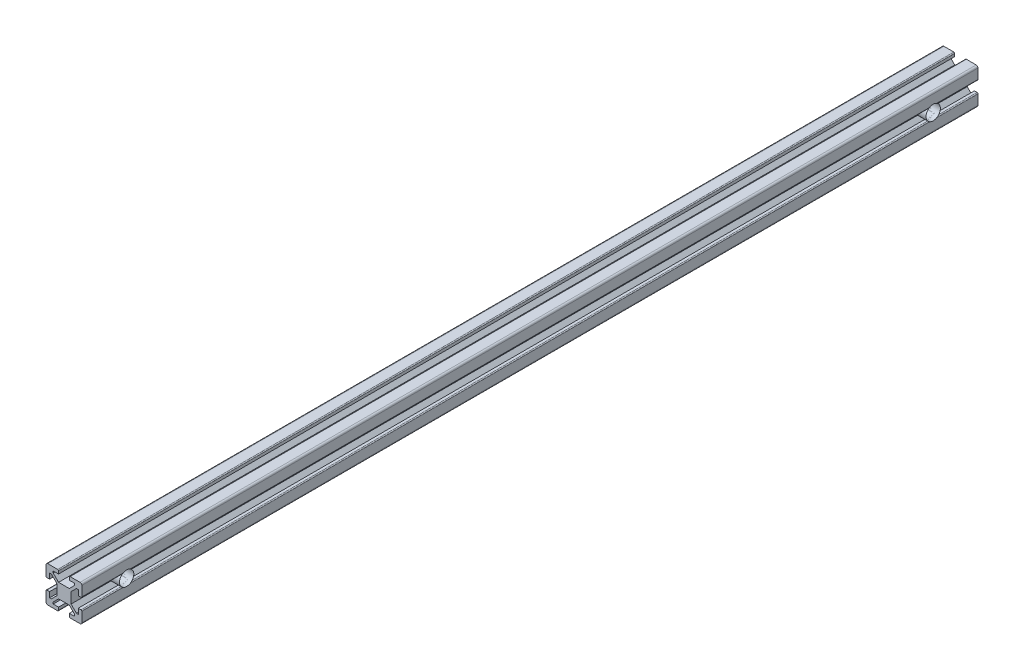
SolidWorks part; units mm, degrees
material "Lega 6061"
ref_plane "Piano frontale" through (0, 0, 0) normal (0, 0, 1) x (1, 0, 0)
ref_plane "Piano superiore" through (0, 0, 0) normal (0, 1, 0) x (1, 0, 0)
ref_plane "Piano destro" through (0, 0, 0) normal (1, 0, 0) x (0, 0, -1)
sketch "Schizzo1" plane through (0, 0, 0) normal (0, 0, 1) x (1, 0, 0)
  line L0 (0, 0) -> (-3.6, 0) construction
  line L1 (0, 0) -> (0, 3.6) construction
  line L3 (-4, -3) -> (-4, 3)
  line L4 (-4, 3) -> (-7, 6)
  line L5 (-7, 6) -> (-8, 6)
  line L6 (-8, 6) -> (-8, 3)
  line L7 (-8, 3) -> (-9.5, 3)
  line L8 (-10, 3.5) -> (-10, 9)
  line L9 (0, 0) -> (-10, 10) construction
  line L12 (-3, 4) -> (-6, 7)
  line L13 (-6, 7) -> (-6, 8)
  line L14 (-6, 8) -> (-3, 8)
  line L15 (-3, 8) -> (-3, 9.5)
  line L16 (-3.5, 10) -> (-9, 10)
  line L17 (0, 0) -> (-10, -10) construction
  line L18 (-3.5, -10) -> (-9, -10)
  line L19 (-3, -8) -> (-3, -9.5)
  line L20 (-6, -8) -> (-3, -8)
  line L21 (-6, -7) -> (-6, -8)
  line L22 (-3, -4) -> (-6, -7)
  line L25 (-10, -3.5) -> (-10, -9)
  line L26 (-8, -3) -> (-9.5, -3)
  line L27 (-8, -6) -> (-8, -3)
  line L28 (-7, -6) -> (-8, -6)
  line L29 (-4, -3) -> (-7, -6)
  line L32 (0, 0) -> (10, -10) construction
  line L33 (0, 0) -> (10, 10) construction
  line L36 (4, -3) -> (7, -6)
  line L37 (7, -6) -> (8, -6)
  line L38 (8, -6) -> (8, -3)
  line L39 (8, -3) -> (9.5, -3)
  line L40 (10, -3.5) -> (10, -9)
  line L43 (3, -4) -> (6, -7)
  line L44 (6, -7) -> (6, -8)
  line L45 (6, -8) -> (3, -8)
  line L46 (3, -8) -> (3, -9.5)
  line L47 (3.5, -10) -> (9, -10)
  line L48 (3.5, 10) -> (9, 10)
  line L49 (3, 8) -> (3, 9.5)
  line L50 (6, 8) -> (3, 8)
  line L51 (6, 7) -> (6, 8)
  line L52 (3, 4) -> (6, 7)
  line L55 (10, 3.5) -> (10, 9)
  line L56 (8, 3) -> (9.5, 3)
  line L57 (8, 6) -> (8, 3)
  line L58 (7, 6) -> (8, 6)
  line L59 (4, 3) -> (7, 6)
  line L60 (-3, 4) -> (3, 4)
  line L62 (-3, -4) -> (3, -4)
  line L63 (4, 3) -> (4, -3)
  arc A0 (-10, 9) -> (-9, 10) centre (-9, 9) cw
  arc A1 (-3, 9.5) -> (-3.5, 10) centre (-3.5, 9.5) ccw
  arc A2 (-9.5, 3) -> (-10, 3.5) centre (-9.5, 3.5) cw
  arc A3 (-9.5, -3) -> (-10, -3.5) centre (-9.5, -3.5) ccw
  arc A4 (-3, -9.5) -> (-3.5, -10) centre (-3.5, -9.5) cw
  arc A5 (-10, -9) -> (-9, -10) centre (-9, -9) ccw
  arc A6 (10, -9) -> (9, -10) centre (9, -9) cw
  arc A7 (3, -9.5) -> (3.5, -10) centre (3.5, -9.5) ccw
  arc A8 (9.5, -3) -> (10, -3.5) centre (9.5, -3.5) cw
  arc A9 (9.5, 3) -> (10, 3.5) centre (9.5, 3.5) ccw
  arc A10 (3, 9.5) -> (3.5, 10) centre (3.5, 9.5) cw
  arc A11 (10, 9) -> (9, 10) centre (9, 9) ccw
  point P24 (-3, 10)
  point P27 (-10, 3)
  point P49 (-10, -3)
  point P50 (-3, -10)
  point P92 (3, -10)
  point P93 (10, -3)
  point P94 (10, 3)
  point P95 (3, 10)
  dimension "D2" = 1
  dimension "D12" = 0.5
  dimension "D3" = 8
  dimension "D6" = 6
  dimension "D7" = 12
  dimension "D8" = 20
  dimension "D9" = 2
  dimension "D10" = 4
  dimension "D11" = 45
extrude "Estrusione-Estrusione1" add sketch "Schizzo1" along normal blind 500
sketch "Schizzo2" plane through (-10, 0, 0) normal (-1, 0, 0) x (0, 0, 1)
  line L1 (0, -3.5) -> (0, -9) construction
  line L2 (250, 9) -> (250, -10) construction
  line L11 (500, -10) -> (0, -10) construction
  line L14 (500, 9) -> (0, 9) construction
  circle A6 centre (25, 0) radius 4.005
  circle A7 centre (475, 0) radius 4.005
  dimension "D2" = 8.01
  dimension "D1" = 25
  dimension "D3" = 10
extrude "Estrusione-Estrusione4" add sketch "Schizzo2" against normal blind 20
sketch "Schizzo6" plane through (-10, 0, 0) normal (-1, 0, 0) x (0, 0, 1)
  circle A0 centre (25, 0) radius 4
  circle A1 centre (475, 0) radius 4
  dimension "D1" = 8
  dimension "D2" = 8
extrude "Taglio-Estrusione20" cut sketch "Schizzo6" against normal blind 20
